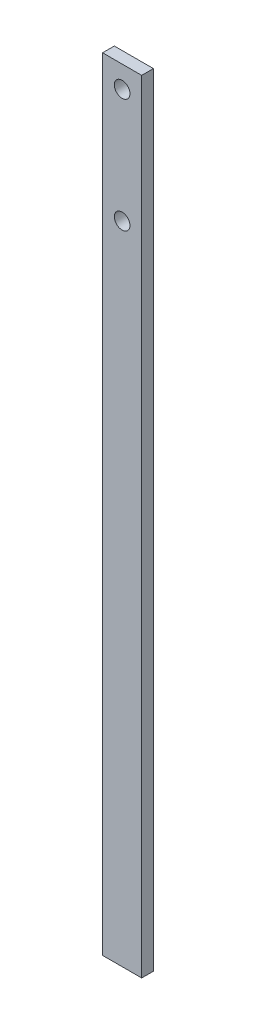
SolidWorks part; units mm, degrees
ref_plane "Front Plane" through (0, 0, 0) normal (0, 0, 1) x (1, 0, 0)
ref_plane "Top Plane" through (0, 0, 0) normal (0, 1, 0) x (1, 0, 0)
ref_plane "Right Plane" through (0, 0, 0) normal (1, 0, 0) x (0, 0, -1)
sketch "Sketch1" plane through (0, 0, 0) normal (0, 0, 1) x (1, 0, 0)
  line L1 (-5, 100) -> (5, 100)
  line L2 (-5, 100) -> (-5, -100)
  line L3 (-5, -100) -> (5, -100)
  line L4 (5, 100) -> (5, -100)
  line L5 (-5, 100) -> (5, -100) construction
  line L6 (-5, -100) -> (5, 100) construction
  point P1 (0, 0)
  dimension "D1" = 10
  dimension "D2" = 200
extrude "Boss-Extrude1" add sketch "Sketch1" along normal blind 3
sketch "Sketch2" plane through (0, 0, 3) normal (0, 0, 1) x (1, 0, 0)
  circle A0 centre (0, 94.4022) radius 2
  circle A1 centre (0, 65.2062) radius 2
  dimension "D1" = 4
extrude "Cut-Extrude1" cut sketch "Sketch2" against normal blind 3
